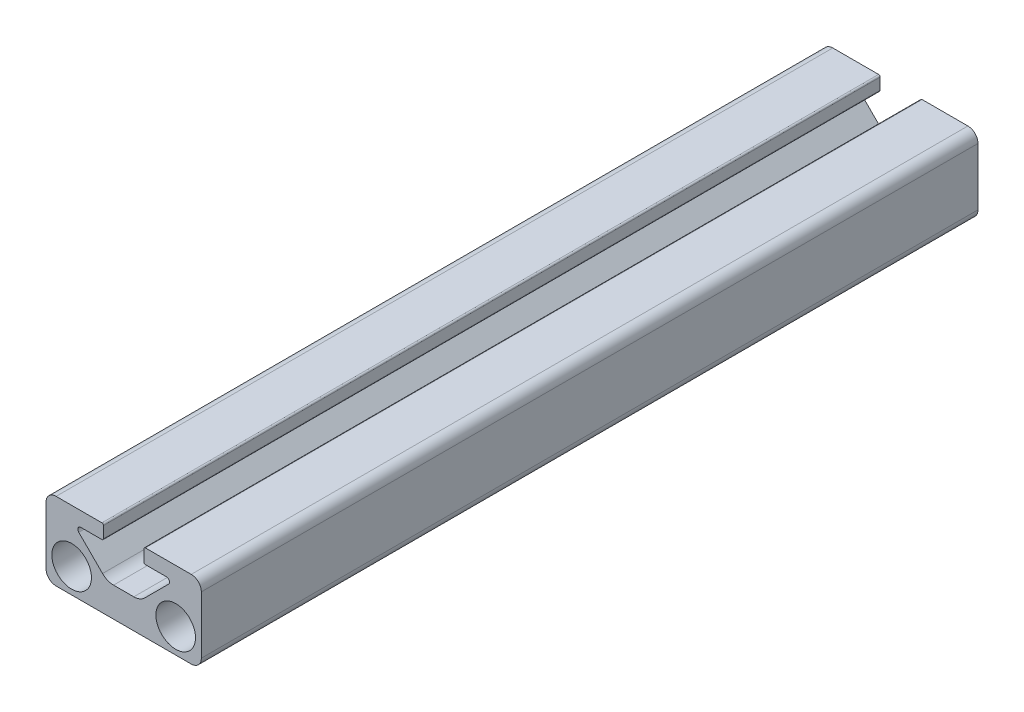
SolidWorks part; units mm, degrees
other "Imported1" parameters "D1"=127, "Length"=127
ref_plane "Front" through (0, 0, 0) normal (0, 0, 1) x (1, 0, 0)
ref_plane "Top" through (0, 0, 0) normal (0, 1, 0) x (1, 0, 0)
ref_plane "Right" through (0, 0, 0) normal (1, 0, 0) x (0, 0, -1)
sketch "Sketch1" plane through (0, 0, 0) normal (0, 0, 1) x (1, 0, 0)
  line L0 (-3.302, 12.7) -> (3.302, 12.7) construction
  line L1 (-7.493, 9.8209) -> (7.493, 9.8209) construction
  line L2 (-11.049, 12.7) -> (-3.302, 12.7)
  line L3 (3.302, 12.7) -> (11.049, 12.7)
  line L4 (11.049, 0) -> (-11.049, 0)
  line L5 (-8.509, 4.064) -> (8.509, 4.064) construction
  line L6 (-3.302, 12.7) -> (-3.302, 10.3289)
  line L7 (3.302, 12.7) -> (3.302, 10.3289)
  line L28 (-12.7, 11.049) -> (-12.7, 1.651)
  line L32 (12.7, 1.651) -> (12.7, 11.049)
  line L35 (3.302, 10.3289) -> (6.985, 10.3289)
  line L36 (7.3442, 9.4617) -> (3.4525, 5.5699)
  line L37 (1.6565, 4.826) -> (-1.6565, 4.826)
  line L38 (-3.4525, 5.5699) -> (-7.3442, 9.4617)
  line L39 (-6.985, 10.3289) -> (-3.302, 10.3289)
  circle A0 centre (-8.509, 4.064) radius 3.2385
  circle A1 centre (8.509, 4.064) radius 3.2385
  arc A36 (-12.7, 1.651) -> (-11.049, 0) centre (-11.049, 1.651) ccw
  arc A41 (11.049, 0) -> (12.7, 1.651) centre (11.049, 1.651) ccw
  arc A42 (12.7, 11.049) -> (11.049, 12.7) centre (11.049, 11.049) ccw
  arc A46 (7.3442, 9.4617) -> (6.985, 10.3289) centre (6.985, 9.8209) ccw
  arc A47 (1.6565, 4.826) -> (3.4525, 5.5699) centre (1.6565, 7.366) ccw
  arc A48 (-3.4525, 5.5699) -> (-1.6565, 4.826) centre (-1.6565, 7.366) ccw
  arc A49 (-6.985, 10.3289) -> (-7.3442, 9.4617) centre (-6.985, 9.8209) ccw
  arc A53 (-11.049, 12.7) -> (-12.7, 11.049) centre (-11.049, 11.049) ccw
  point P5 (0, 4.064)
  point P8 (0, 0)
  point P10 (0, 4.826)
  point P11 (0, 9.8209)
  point P13 (0, 12.7)
  dimension "D6" = 1.651
  dimension "D7" = 0.508
  dimension "D8" = 8.636
  dimension "D9" = 6.477
  dimension "D12" = 2.54
  dimension "D1" = 6.604
  dimension "D2" = 14.986
  dimension "D3" = 17.018
  dimension "D4" = 25.4
  dimension "D5" = 12.7
  dimension "D10" = 7.874
  dimension "D11" = 2.3711
  dimension "D13" = 45
sketch "Sketch2" plane through (0, 0, 0) normal (1, 0, 0) x (0, 0, -1)
  line L0 (63.5, 0) -> (-63.5, 0) construction
  point P4 (0, 0)
sketch "Sketch3" plane through (0, 0, 0) normal (0, 0, 1) x (1, 0, 0)
  line L0 (-11.049, 12.7) -> (-3.302, 12.7) construction
  line L1 (-3.302, 12.7) -> (-3.302, 10.3289) construction
  line L2 (-6.985, 10.3289) -> (-3.302, 10.3289) construction
  line L3 (-3.4525, 5.5699) -> (-7.3442, 9.4617) construction
  line L4 (1.6565, 4.826) -> (-1.6565, 4.826) construction
  line L5 (7.3442, 9.4617) -> (3.4525, 5.5699) construction
  line L6 (3.302, 10.3289) -> (6.985, 10.3289) construction
  line L7 (3.302, 12.7) -> (3.302, 10.3289) construction
  line L8 (3.302, 12.7) -> (11.049, 12.7) construction
  line L9 (12.7, 1.651) -> (12.7, 11.049) construction
  line L10 (11.049, 0) -> (-11.049, 0) construction
  line L11 (-12.7, 11.049) -> (-12.7, 1.651) construction
  line L12 (-11.049, 12.7) -> (-3.302, 12.7)
  line L13 (-3.302, 12.7) -> (-3.302, 10.3289)
  line L14 (-6.985, 10.3289) -> (-3.302, 10.3289)
  line L15 (-3.4525, 5.5699) -> (-7.3442, 9.4617)
  line L16 (1.6565, 4.826) -> (-1.6565, 4.826)
  line L17 (7.3442, 9.4617) -> (3.4525, 5.5699)
  line L18 (3.302, 10.3289) -> (6.985, 10.3289)
  line L19 (3.302, 12.7) -> (3.302, 10.3289)
  line L20 (3.302, 12.7) -> (11.049, 12.7)
  line L21 (12.7, 1.651) -> (12.7, 11.049)
  line L22 (11.049, 0) -> (-11.049, 0)
  line L23 (-12.7, 11.049) -> (-12.7, 1.651)
  circle A0 centre (8.509, 4.064) radius 3.2385 construction
  circle A1 centre (-8.509, 4.064) radius 3.2385 construction
  arc A2 (-6.985, 10.3289) -> (-7.3442, 9.4617) centre (-6.985, 9.8209) ccw construction
  arc A3 (-3.4525, 5.5699) -> (-1.6565, 4.826) centre (-1.6565, 7.366) ccw construction
  arc A4 (1.6565, 4.826) -> (3.4525, 5.5699) centre (1.6565, 7.366) ccw construction
  arc A5 (7.3442, 9.4617) -> (6.985, 10.3289) centre (6.985, 9.8209) ccw construction
  arc A6 (12.7, 11.049) -> (11.049, 12.7) centre (11.049, 11.049) ccw construction
  arc A7 (11.049, 0) -> (12.7, 1.651) centre (11.049, 1.651) ccw construction
  arc A8 (-12.7, 1.651) -> (-11.049, 0) centre (-11.049, 1.651) ccw construction
  arc A9 (-11.049, 12.7) -> (-12.7, 11.049) centre (-11.049, 11.049) ccw construction
  circle A10 centre (8.509, 4.064) radius 3.2385
  circle A11 centre (-8.509, 4.064) radius 3.2385
  arc A12 (-6.985, 10.3289) -> (-7.3442, 9.4617) centre (-6.985, 9.8209) ccw
  arc A13 (-3.4525, 5.5699) -> (-1.6565, 4.826) centre (-1.6565, 7.366) ccw
  arc A14 (1.6565, 4.826) -> (3.4525, 5.5699) centre (1.6565, 7.366) ccw
  arc A15 (7.3442, 9.4617) -> (6.985, 10.3289) centre (6.985, 9.8209) ccw
  arc A16 (12.7, 11.049) -> (11.049, 12.7) centre (11.049, 11.049) ccw
  arc A17 (11.049, 0) -> (12.7, 1.651) centre (11.049, 1.651) ccw
  arc A18 (-12.7, 1.651) -> (-11.049, 0) centre (-11.049, 1.651) ccw
  arc A19 (-11.049, 12.7) -> (-12.7, 11.049) centre (-11.049, 11.049) ccw
extrude "Boss-Extrude1" add sketch "Sketch3" along normal mid plane 127
fillet "Fillet1" radius 0.254 4 edges at (3.302, 10.3289, 0) (3.302, 12.7, 0) (-3.302, 10.3289, 0) (-3.302, 12.7, 0)
equation "\"D1@Boss-Extrude1\"=\"Length@Sketch2\""
